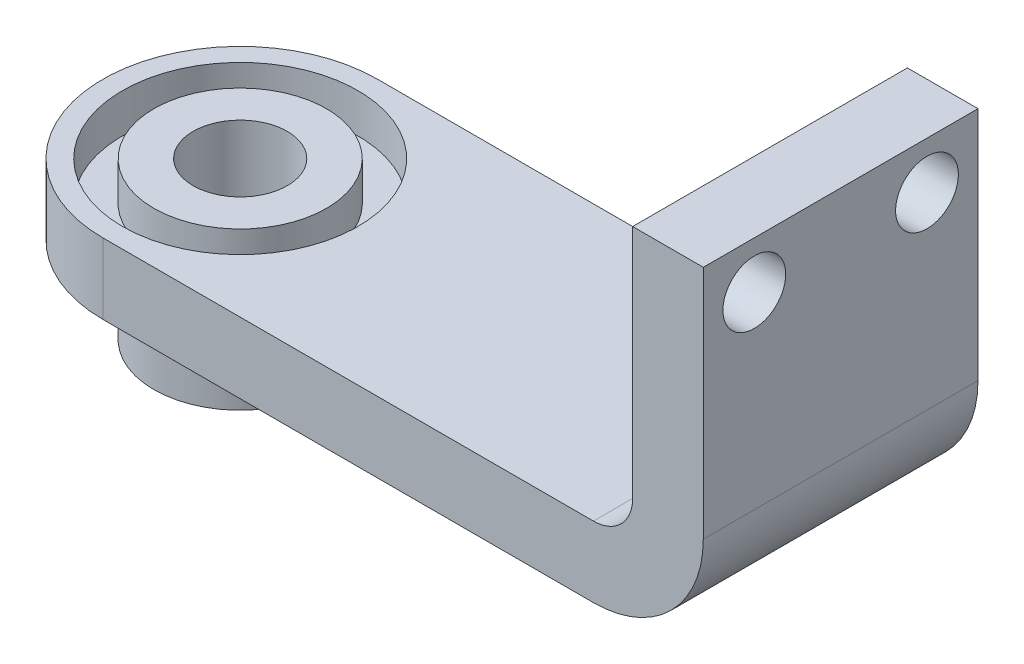
SolidWorks part; units mm, degrees
ref_plane "Front Plane" through (0, 0, 0) normal (0, 0, 1) x (1, 0, 0)
ref_plane "Top Plane" through (0, 0, 0) normal (0, 1, 0) x (1, 0, 0)
ref_plane "Right Plane" through (0, 0, 0) normal (1, 0, 0) x (0, 0, -1)
sketch "Sketch5" plane through (0, 0, 0) normal (0, 0, 1) x (1, 0, 0)
  line L0 (-17.5, 0) -> (-17.5, -9)
  line L1 (-17.5, -9) -> (45, -9)
  line L3 (0, 9.9991) -> (0, -14.722) construction
  line L4 (-38.9997, 0) -> (82.3011, 0) construction
  line L5 (59, 5) -> (59, 35)
  line L6 (59, 35) -> (50, 35)
  line L7 (50, 35) -> (50, 5)
  line L9 (-17.5, 0) -> (45, 0)
  arc A0 (45, -9) -> (59, 5) centre (45, 5) ccw
  arc A1 (45, 0) -> (50, 5) centre (45, 5) ccw
  dimension "D1" = 5
  dimension "D2" = 14
  dimension "D3" = 9
  dimension "D4" = 9
  dimension "D5" = 35
  dimension "D6" = 17.5
  dimension "D7" = 76.5
extrude "Boss-Extrude1" add sketch "Sketch5" against normal blind 35
sketch "Sketch8" plane through (0, 0, 0) normal (0, 1, 0) x (1, 0, 0)
  line L1 (0, 40.76) -> (0, -33.9623) construction
  line L2 (-47.3529, 0) -> (101.3368, 0) construction
  line L8 (-17.5, 0) -> (45, 0)
  line L9 (45, 0) -> (45, 35)
  line L10 (45, 35) -> (-17.5, 35)
  line L11 (-17.5, 35) -> (-17.5, 0)
  line L15 (-17.5, 35) -> (-17.5, 0)
  arc A1 (-17.5, 35) -> (-17.5, 0) centre (-17.5, 17.5) ccw
  dimension "D1" = 17.5
  dimension "D2" = 0
extrude "Boss-Extrude2" add sketch "Sketch8" against normal up to surface (9 mm away) up to face at (13.75, -9, -17.5)
sketch "Sketch12" plane through (0, 0, 0) normal (0, 1, 0) x (1, 0, 0)
  line L1 (0, 51.355) -> (0, -24.7501) construction
  line L2 (-58.6557, 0) -> (96.6055, 0) construction
  circle A2 centre (-17.5, 17.5) radius 11
  circle A5 centre (-17.5, 17.5) radius 6
  dimension "D1" = 22
  dimension "D2" = 12
  dimension "D3" = 17.5
  dimension "D4" = 17.5
extrude "Boss-Extrude3" add sketch "Sketch12" against normal blind 20 separate body
sketch "Sketch7" plane through (50, 0, 0) normal (-1, 0, 0) x (0, 0, 1)
  line L0 (-41.0089, 29) -> (14.1765, 29) construction
  line L2 (-35, 35) -> (0, 35) construction
  line L3 (0, 5) -> (0, 35) construction
  circle A0 centre (-28.5021, 29) radius 4
  circle A1 centre (-6.5, 29) radius 4
  dimension "D3" = 8
  dimension "D4" = 8
  dimension "D1" = 22.0021
  dimension "D2" = 6
  dimension "D5" = 6.5
extrude "Cut-Extrude1" cut sketch "Sketch7" against normal blind 35 contours A0 | A1
sketch "Sketch9" plane through (0, 0, 0) normal (0, 1, 0) x (1, 0, 0)
  line L0 (-17.5, 35) -> (-17.5, 0) construction
  line L1 (-35, 17.5) -> (36.969, 17.5) construction
  arc A2 (-17.5, 35) -> (-17.5, 0) centre (-17.5, 17.5) ccw construction
  circle A3 centre (-17.5, 17.5) radius 15
  dimension "D1" = 30
extrude "Cut-Extrude2" cut sketch "Sketch9" against normal blind 5
sketch "Sketch10" plane through (0, -5, 0) normal (0, 1, 0) x (1, 0, 0)
  line L0 (-17.5, 35) -> (-17.5, 0) construction
  line L2 (-35, 17.5) -> (-2.5, 17.5) construction
  arc A1 (-17.5, 35) -> (-17.5, 0) centre (-17.5, 17.5) ccw construction
  circle A2 centre (-17.5, 17.5) radius 15 construction
  circle A3 centre (-17.5, 17.5) radius 11
  dimension "D1" = 22
extrude "Cut-Extrude3" cut sketch "Sketch10" against normal blind 25
